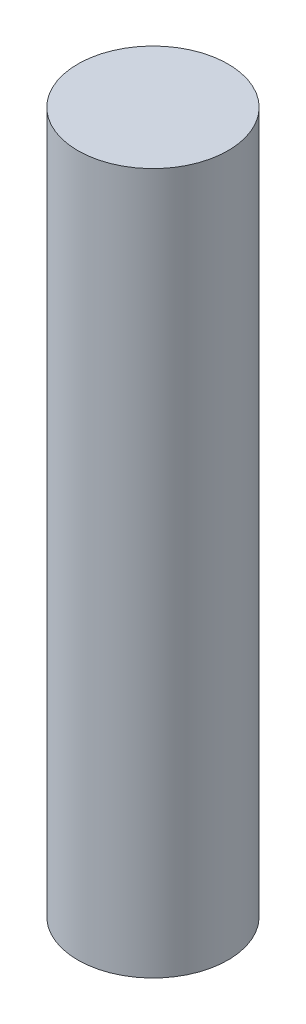
SolidWorks part; units mm, degrees
ref_plane "Front" through (0, 0, 0) normal (0, 0, 1) x (1, 0, 0)
ref_plane "Top" through (0, 0, 0) normal (0, 1, 0) x (1, 0, 0)
ref_plane "Right" through (0, 0, 0) normal (1, 0, 0) x (0, 0, -1)
sketch "Sketch2" plane through (0, 0, 0) normal (0, 1, 0) x (1, 0, 0)
  circle A0 centre (0, 0) radius 1.5
  dimension "D1" = 3
extrude "Boss-Extrude1" add sketch "Sketch2" along normal blind 14
